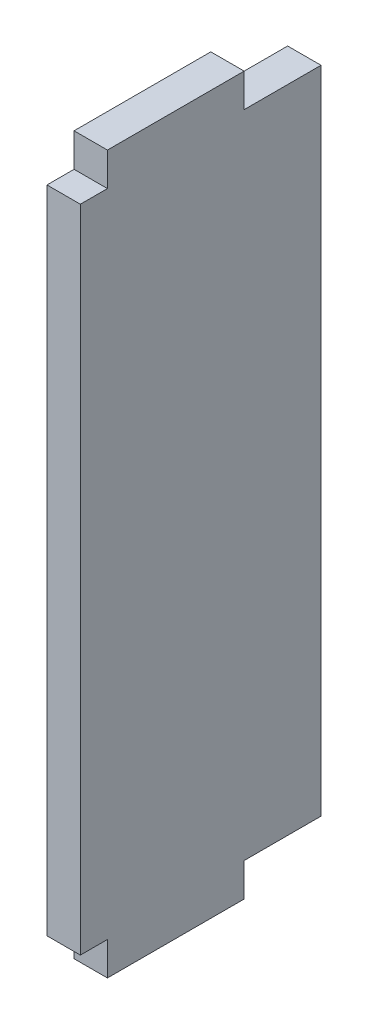
SolidWorks part; units mm, degrees
ref_plane "Alzado" through (0, 0, 0) normal (0, 0, 1) x (1, 0, 0)
ref_plane "Planta" through (0, 0, 0) normal (0, 1, 0) x (1, 0, 0)
ref_plane "Vista lateral" through (0, 0, 0) normal (1, 0, 0) x (0, 0, -1)
sketch "Croquis1" plane through (0, 0, 0) normal (1, 0, 0) x (0, 0, -1)
  line L0 (3.18, -23.78) -> (8.8, -23.78)
  line L1 (-8.8, -23.78) -> (-6.82, -23.78)
  line L2 (-8.8, -23.78) -> (-8.8, 23.78)
  line L3 (-8.8, 23.78) -> (-6.82, 23.78)
  line L4 (8.8, -23.78) -> (8.8, 23.78)
  line L5 (-8.8, -23.78) -> (8.8, 23.78) construction
  line L6 (-8.8, 23.78) -> (8.8, -23.78) construction
  line L7 (0, 0) -> (-5.5371, 0) construction
  line L8 (3.18, -23.78) -> (3.18, -26.22)
  line L9 (3.18, -26.22) -> (-6.82, -26.22)
  line L10 (-6.82, -23.78) -> (-6.82, -26.22)
  line L11 (-6.82, 23.78) -> (-6.82, 26.22)
  line L12 (3.18, 26.22) -> (-6.82, 26.22)
  line L13 (3.18, 23.78) -> (3.18, 26.22)
  line L14 (3.18, 23.78) -> (8.8, 23.78)
  point P0 (0, 0)
  dimension "D1" = 47.56
  dimension "D2" = 17.6
  dimension "D3" = 5.62
  dimension "D4" = 10
  dimension "D5" = 2.44
extrude "Saliente-Extruir1" add sketch "Croquis1" along normal blind 2.44
